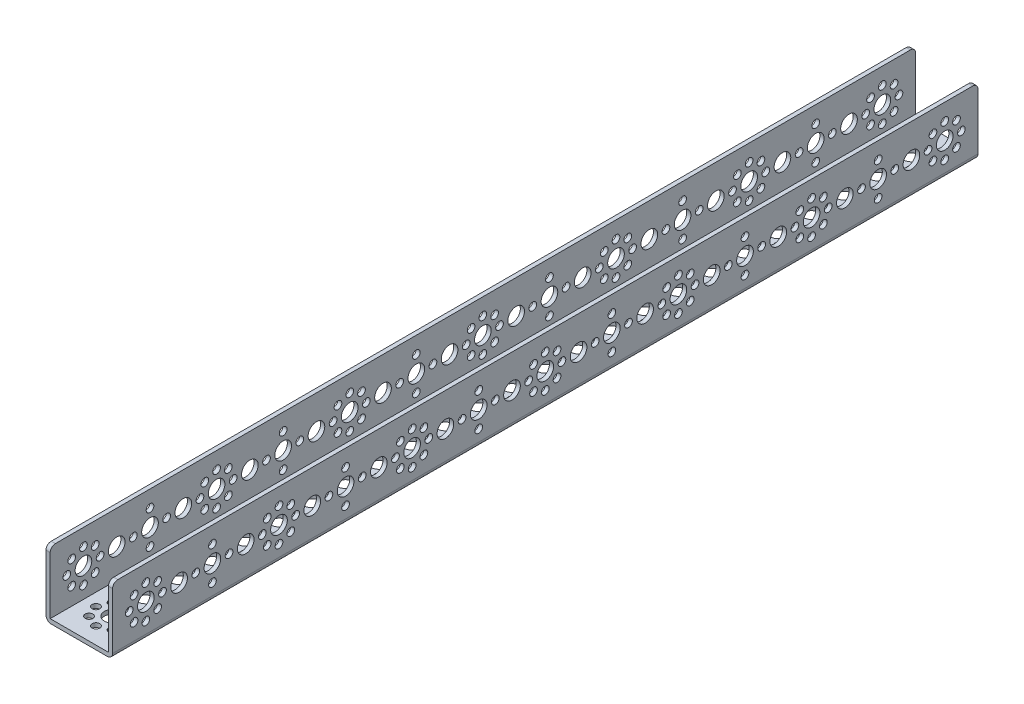
SolidWorks part; units mm, degrees
material "2024 Alloy"
ref_plane "Front Plane" through (0, 0, 0) normal (0, 0, 1) x (1, 0, 0)
ref_plane "Top Plane" through (0, 0, 0) normal (0, 1, 0) x (1, 0, 0)
ref_plane "Right Plane" through (0, 0, 0) normal (1, 0, 0) x (0, 0, -1)
ref_plane "Plane1" through (-16, 0, 0) normal (-1, 0, 0) x (0, -1, 0)
sketch "Sketch1" plane through (-16, 0, 0) normal (-1, 0, 0) x (0, -1, 0)
  line L0 (-32, -400) -> (0, -400)
  line L1 (0, -400) -> (0, 16)
  line L2 (0, 16) -> (-32, 16)
  line L3 (-32, 16) -> (-32, -400)
extrude "Boss-Extrude1" add sketch "Sketch1" against normal blind 32
sketch "Sketch2" plane through (0, 0, 16) normal (0, 0, 1) x (1, 0, 0)
  line L0 (14, 32) -> (-14, 32)
  line L1 (-14, 32) -> (-14, 2)
  line L2 (-14, 2) -> (14, 2)
  line L3 (14, 2) -> (14, 32)
extrude "Cut-Extrude1" cut sketch "Sketch2" against normal through all
hole_wizard "Ø8.0 (8) Diameter Hole1" positions "Sketch4" profile "Sketch3" hole size "Ø8.0" standard "ANSI Metric"
sketch "Sketch4" plane through (14, 0, 0) normal (-1, 0, 0) x (0, 0, 1)
  point P0 (-32, 16)
sketch "Sketch3" plane through (14, 16, -32) normal (0, 1, 0) x (0, 0, 1)
  line L0 (0, 0) -> (0, 2)
  line L1 (0, 2) -> (4, 2)
  line L2 (4, 2) -> (4, 0)
  line L5 (4, 0) -> (0, 0)
  line L11 (0, -6.35) -> (0, 107.95) construction
  dimension "Thru Hole Dia." = 8
  dimension "Thru Hole Depth" = 2
hole_wizard "Ø8.0 (8) Diameter Hole2" positions "Sketch6" profile "Sketch5" hole size "Ø8.0" standard "ANSI Metric"
sketch "Sketch6" plane through (16, 0, 0) normal (1, 0, 0) x (0, 0, -1)
  point P0 (64, 16)
  point P1 (128, 16)
  point P2 (192, 16)
  point P3 (256, 16)
  point P4 (320, 16)
  point P5 (384, 16)
  point P6 (96, 16)
  point P7 (160, 16)
  point P8 (224, 16)
  point P9 (288, 16)
  point P10 (352, 16)
  point P11 (16, 16)
  point P12 (48, 16)
  point P13 (80, 16)
  point P14 (112, 16)
  point P15 (144, 16)
  point P16 (176, 16)
  point P17 (208, 16)
  point P18 (240, 16)
  point P19 (0, 16)
  point P20 (272, 16)
  point P21 (304, 16)
  point P22 (336, 16)
  point P23 (368, 16)
sketch "Sketch5" plane through (16, 16, -64) normal (0, 1, 0) x (0, 0, -1)
  line L0 (0, 0) -> (0, 2)
  line L1 (0, 2) -> (4, 2)
  line L2 (4, 2) -> (4, 0)
  line L5 (4, 0) -> (0, 0)
  line L11 (0, -6.35) -> (0, 107.95) construction
  dimension "Thru Hole Dia." = 8
  dimension "Thru Hole Depth" = 2
hole_wizard "Ø3.7 (3.7) Diameter Hole1" positions "Sketch8" profile "Sketch7" hole size "Ø3.7" standard "ANSI Metric"
sketch "Sketch8" plane through (16, 0, 0) normal (1, 0, 0) x (0, 0, -1)
  point P0 (0, 24)
  point P1 (0, 8)
  point P2 (8, 16)
  point P3 (-8, 16)
  point P4 (5.6569, 21.6569)
  point P5 (-5.6569, 21.6569)
  point P6 (-5.6569, 10.3431)
  point P7 (5.6569, 10.3431)
  point P8 (64, 24)
  point P9 (64, 8)
  point P10 (72, 16)
  point P11 (56, 16)
  point P12 (69.6569, 21.6569)
  point P13 (58.3431, 21.6569)
  point P14 (58.3431, 10.3431)
  point P15 (69.6569, 10.3431)
  point P16 (128, 24)
  point P17 (128, 8)
  point P18 (136, 16)
  point P19 (120, 16)
  point P20 (133.6569, 21.6569)
  point P21 (122.3431, 21.6569)
  point P22 (122.3431, 10.3431)
  point P23 (133.6569, 10.3431)
  point P24 (192, 24)
  point P25 (192, 8)
  point P26 (200, 16)
  point P27 (184, 16)
  point P28 (197.6569, 21.6569)
  point P29 (186.3431, 21.6569)
  point P30 (186.3431, 10.3431)
  point P31 (197.6569, 10.3431)
  point P32 (256, 24)
  point P33 (256, 8)
  point P34 (264, 16)
  point P35 (248, 16)
  point P36 (261.6569, 21.6569)
  point P37 (250.3431, 21.6569)
  point P38 (250.3431, 10.3431)
  point P39 (261.6569, 10.3431)
  point P40 (320, 24)
  point P41 (320, 8)
  point P42 (328, 16)
  point P43 (312, 16)
  point P44 (325.6569, 21.6569)
  point P45 (314.3431, 21.6569)
  point P46 (314.3431, 10.3431)
  point P47 (325.6569, 10.3431)
  point P48 (384, 24)
  point P49 (384, 8)
  point P50 (392, 16)
  point P51 (376, 16)
  point P52 (389.6569, 21.6569)
  point P53 (378.3431, 21.6569)
  point P54 (378.3431, 10.3431)
  point P55 (389.6569, 10.3431)
  point P56 (32, 24)
  point P57 (40, 16)
  point P58 (32, 8)
  point P59 (24, 16)
  point P60 (96, 24)
  point P61 (104, 16)
  point P62 (96, 8)
  point P63 (88, 16)
  point P64 (160, 24)
  point P65 (168, 16)
  point P66 (160, 8)
  point P67 (152, 16)
  point P68 (224, 24)
  point P69 (232, 16)
  point P70 (224, 8)
  point P71 (216, 16)
  point P72 (288, 24)
  point P73 (296, 16)
  point P74 (288, 8)
  point P75 (280, 16)
  point P76 (352, 24)
  point P77 (360, 16)
  point P78 (352, 8)
  point P79 (344, 16)
sketch "Sketch7" plane through (16, 24, 0) normal (0, 1, 0) x (0, 0, -1)
  line L0 (0, 0) -> (0, 2)
  line L1 (0, 2) -> (1.85, 2)
  line L2 (1.85, 2) -> (1.85, 0)
  line L5 (1.85, 0) -> (0, 0)
  line L11 (0, -6.35) -> (0, 107.95) construction
  dimension "Thru Hole Dia." = 3.7
  dimension "Thru Hole Depth" = 2
hole_wizard "Ø3.7 (3.7) Diameter Hole2" positions "Sketch10" profile "Sketch9" hole size "Ø3.7" standard "ANSI Metric"
sketch "Sketch10" plane through (0, 0, 0) normal (0, -1, 0) x (-1, 0, 0)
  point P0 (8, 0)
  point P1 (5.6569, 5.6569)
  point P2 (0, 8)
  point P3 (-5.6569, 5.6569)
  point P4 (-8, 0)
  point P5 (-5.6569, -5.6569)
  point P6 (0, -8)
  point P7 (5.6569, -5.6569)
  point P8 (8, 64)
  point P9 (5.6569, 69.6569)
  point P10 (0, 72)
  point P11 (-5.6569, 69.6569)
  point P12 (-8, 64)
  point P13 (-5.6569, 58.3431)
  point P14 (0, 56)
  point P15 (5.6569, 58.3431)
  point P16 (8, 128)
  point P17 (5.6569, 133.6569)
  point P18 (0, 136)
  point P19 (-5.6569, 133.6569)
  point P20 (-8, 128)
  point P21 (-5.6569, 122.3431)
  point P22 (0, 120)
  point P23 (5.6569, 122.3431)
  point P24 (8, 192)
  point P25 (5.6569, 197.6569)
  point P26 (0, 200)
  point P27 (-5.6569, 197.6569)
  point P28 (-8, 192)
  point P29 (-5.6569, 186.3431)
  point P30 (0, 184)
  point P31 (5.6569, 186.3431)
  point P32 (8, 256)
  point P33 (5.6569, 261.6569)
  point P34 (0, 264)
  point P35 (-5.6569, 261.6569)
  point P36 (-8, 256)
  point P37 (-5.6569, 250.3431)
  point P38 (0, 248)
  point P39 (5.6569, 250.3431)
  point P40 (8, 320)
  point P41 (5.6569, 325.6569)
  point P42 (0, 328)
  point P43 (-5.6569, 325.6569)
  point P44 (-8, 320)
  point P45 (-5.6569, 314.3431)
  point P46 (0, 312)
  point P47 (5.6569, 314.3431)
  point P48 (8, 384)
  point P49 (5.6569, 389.6569)
  point P50 (0, 392)
  point P51 (-5.6569, 389.6569)
  point P52 (-8, 384)
  point P53 (-5.6569, 378.3431)
  point P54 (0, 376)
  point P55 (5.6569, 378.3431)
  point P56 (8, 32)
  point P57 (0, 40)
  point P58 (-8, 32)
  point P59 (0, 24)
  point P60 (8, 96)
  point P61 (0, 104)
  point P62 (-8, 96)
  point P63 (0, 88)
  point P64 (8, 160)
  point P65 (0, 168)
  point P66 (-8, 160)
  point P67 (0, 152)
  point P68 (8, 224)
  point P69 (0, 232)
  point P70 (-8, 224)
  point P71 (0, 216)
  point P72 (8, 288)
  point P73 (0, 296)
  point P74 (-8, 288)
  point P75 (0, 280)
  point P76 (8, 352)
  point P77 (0, 360)
  point P78 (-8, 352)
  point P79 (0, 344)
sketch "Sketch9" plane through (-8, 0, 0) normal (1, 0, 0) x (0, 0, -1)
  line L0 (0, 0) -> (0, 32)
  line L1 (0, 32) -> (1.85, 32)
  line L2 (1.85, 32) -> (1.85, 0)
  line L5 (1.85, 0) -> (0, 0)
  line L11 (0, -6.35) -> (0, 107.95) construction
  dimension "Thru Hole Dia." = 3.7
  dimension "Thru Hole Depth" = 32
hole_wizard "Ø8.0 (8) Diameter Hole3" positions "Sketch12" profile "Sketch11" hole size "Ø8.0" standard "ANSI Metric"
sketch "Sketch12" plane through (0, 0, 0) normal (0, -1, 0) x (-1, 0, 0)
  point P0 (0, 0)
  point P1 (0, 64)
  point P2 (0, 128)
  point P3 (0, 192)
  point P4 (0, 256)
  point P5 (0, 320)
  point P6 (0, 384)
  point P7 (0, 32)
  point P8 (0, 96)
  point P9 (0, 160)
  point P10 (0, 224)
  point P11 (0, 288)
  point P12 (0, 352)
  point P13 (0, 16)
  point P14 (0, 48)
  point P15 (0, 80)
  point P16 (0, 112)
  point P17 (0, 144)
  point P18 (0, 176)
  point P19 (0, 208)
  point P20 (0, 240)
  point P21 (0, 272)
  point P22 (0, 304)
  point P23 (0, 336)
  point P24 (0, 368)
sketch "Sketch11" plane through (0, 0, 0) normal (1, 0, 0) x (0, 0, -1)
  line L0 (0, 0) -> (0, 32)
  line L1 (0, 32) -> (4, 32)
  line L2 (4, 32) -> (4, 0)
  line L5 (4, 0) -> (0, 0)
  line L11 (0, -6.35) -> (0, 107.95) construction
  dimension "Thru Hole Dia." = 8
  dimension "Thru Hole Depth" = 32
hole_wizard "Ø8.0 (8) Diameter Hole4" positions "Sketch14" profile "Sketch13" hole size "Ø8.0" standard "ANSI Metric"
sketch "Sketch14" plane through (-16, 0, 0) normal (-1, 0, 0) x (0, 0, 1)
  point P0 (-64, 16)
  point P1 (-128, 16)
  point P2 (-192, 16)
  point P3 (-256, 16)
  point P4 (-320, 16)
  point P5 (-384, 16)
  point P6 (-32, 16)
  point P7 (-96, 16)
  point P8 (-160, 16)
  point P9 (-224, 16)
  point P10 (-288, 16)
  point P11 (-352, 16)
  point P12 (-16, 16)
  point P13 (-48, 16)
  point P14 (-80, 16)
  point P15 (-112, 16)
  point P16 (-144, 16)
  point P17 (-176, 16)
  point P18 (-208, 16)
  point P19 (-240, 16)
  point P20 (0, 16)
  point P21 (-272, 16)
  point P22 (-304, 16)
  point P23 (-336, 16)
  point P24 (-368, 16)
sketch "Sketch13" plane through (-16, 16, -64) normal (0, 1, 0) x (0, 0, 1)
  line L0 (0, 0) -> (0, 32)
  line L1 (0, 32) -> (4, 32)
  line L2 (4, 32) -> (4, 0)
  line L5 (4, 0) -> (0, 0)
  line L11 (0, -6.35) -> (0, 107.95) construction
  dimension "Thru Hole Dia." = 8
  dimension "Thru Hole Depth" = 32
hole_wizard "Ø3.7 (3.7) Diameter Hole3" positions "Sketch16" profile "Sketch15" hole size "Ø3.7" standard "ANSI Metric"
sketch "Sketch16" plane through (-16, 0, 0) normal (-1, 0, 0) x (0, 0, 1)
  point P0 (0, 24)
  point P1 (0, 8)
  point P2 (-8, 16)
  point P3 (8, 16)
  point P4 (-5.6569, 21.6569)
  point P5 (5.6569, 21.6569)
  point P6 (5.6569, 10.3431)
  point P7 (-5.6569, 10.3431)
  point P8 (-64, 24)
  point P9 (-64, 8)
  point P10 (-72, 16)
  point P11 (-56, 16)
  point P12 (-69.6569, 21.6569)
  point P13 (-58.3431, 21.6569)
  point P14 (-58.3431, 10.3431)
  point P15 (-69.6569, 10.3431)
  point P16 (-128, 24)
  point P17 (-128, 8)
  point P18 (-136, 16)
  point P19 (-120, 16)
  point P20 (-133.6569, 21.6569)
  point P21 (-122.3431, 21.6569)
  point P22 (-122.3431, 10.3431)
  point P23 (-133.6569, 10.3431)
  point P24 (-192, 24)
  point P25 (-192, 8)
  point P26 (-200, 16)
  point P27 (-184, 16)
  point P28 (-197.6569, 21.6569)
  point P29 (-186.3431, 21.6569)
  point P30 (-186.3431, 10.3431)
  point P31 (-197.6569, 10.3431)
  point P32 (-256, 24)
  point P33 (-256, 8)
  point P34 (-264, 16)
  point P35 (-248, 16)
  point P36 (-261.6569, 21.6569)
  point P37 (-250.3431, 21.6569)
  point P38 (-250.3431, 10.3431)
  point P39 (-261.6569, 10.3431)
  point P40 (-320, 24)
  point P41 (-320, 8)
  point P42 (-328, 16)
  point P43 (-312, 16)
  point P44 (-325.6569, 21.6569)
  point P45 (-314.3431, 21.6569)
  point P46 (-314.3431, 10.3431)
  point P47 (-325.6569, 10.3431)
  point P48 (-384, 24)
  point P49 (-384, 8)
  point P50 (-392, 16)
  point P51 (-376, 16)
  point P52 (-389.6569, 21.6569)
  point P53 (-378.3431, 21.6569)
  point P54 (-378.3431, 10.3431)
  point P55 (-389.6569, 10.3431)
  point P56 (-32, 24)
  point P57 (-40, 16)
  point P58 (-32, 8)
  point P59 (-24, 16)
  point P60 (-96, 24)
  point P61 (-104, 16)
  point P62 (-96, 8)
  point P63 (-88, 16)
  point P64 (-160, 24)
  point P65 (-168, 16)
  point P66 (-160, 8)
  point P67 (-152, 16)
  point P68 (-224, 24)
  point P69 (-232, 16)
  point P70 (-224, 8)
  point P71 (-216, 16)
  point P72 (-288, 24)
  point P73 (-296, 16)
  point P74 (-288, 8)
  point P75 (-280, 16)
  point P76 (-352, 24)
  point P77 (-360, 16)
  point P78 (-352, 8)
  point P79 (-344, 16)
sketch "Sketch15" plane through (-16, 24, 0) normal (0, 1, 0) x (0, 0, 1)
  line L0 (0, 0) -> (0, 32)
  line L1 (0, 32) -> (1.85, 32)
  line L2 (1.85, 32) -> (1.85, 0)
  line L5 (1.85, 0) -> (0, 0)
  line L11 (0, -6.35) -> (0, 107.95) construction
  dimension "Thru Hole Dia." = 3.7
  dimension "Thru Hole Depth" = 32
fillet "Fillet1" radius 2.5 6 edges at (16, 0, -192) (15, 32, -400) (15, 32, 16) (-15, 32, 16) (-15, 32, -400) (-16, 0, -192)
